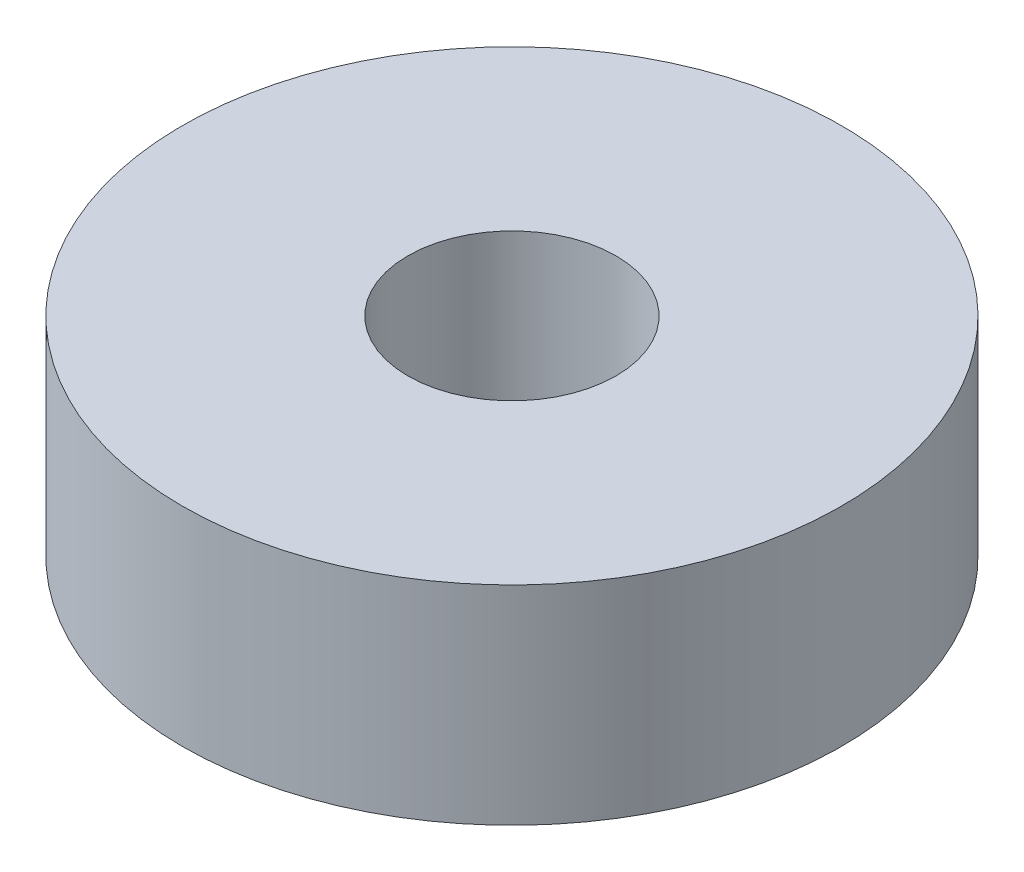
SolidWorks part; units mm, degrees
material "1060 Alloy"
ref_plane "Front Plane" through (0, 0, 0) normal (0, 0, 1) x (1, 0, 0)
ref_plane "Top Plane" through (0, 0, 0) normal (0, 1, 0) x (1, 0, 0)
ref_plane "Right Plane" through (0, 0, 0) normal (1, 0, 0) x (0, 0, -1)
sketch "Sketch1" plane through (0, 0, 0) normal (0, 1, 0) x (1, 0, 0)
  circle A0 centre (0, 0) radius 3
  circle A1 centre (0, 0) radius 9.5
  dimension "D1" = 6
  dimension "D2" = 19
extrude "Boss-Extrude1" add sketch "Sketch1" along normal blind 6
